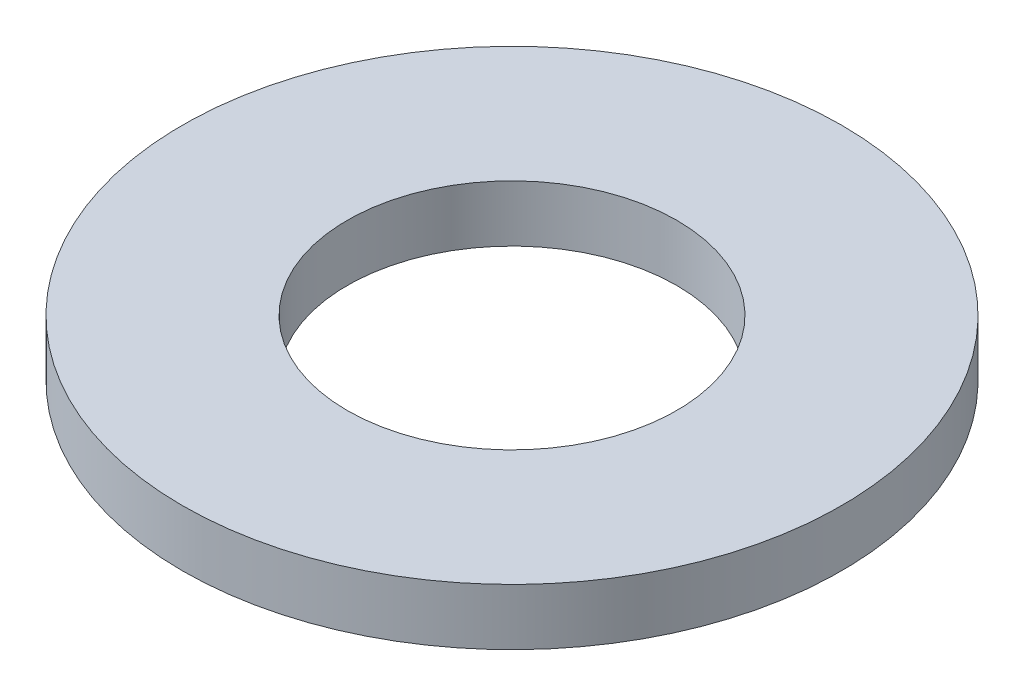
SolidWorks part; units mm, degrees
ref_plane "Front" through (0, 0, 0) normal (0, 0, 1) x (1, 0, 0)
ref_plane "Top" through (0, 0, 0) normal (0, 1, 0) x (1, 0, 0)
ref_plane "Right" through (0, 0, 0) normal (1, 0, 0) x (0, 0, -1)
sketch "Sketch1" plane through (0, 0, 0) normal (0, 1, 0) x (1, 0, 0)
  circle A0 centre (0, 0) radius 35
  circle A1 centre (0, 0) radius 17.5
  dimension "D1" = 70
  dimension "D2" = 35
extrude "Boss-Extrude1" add sketch "Sketch1" along normal blind 6
